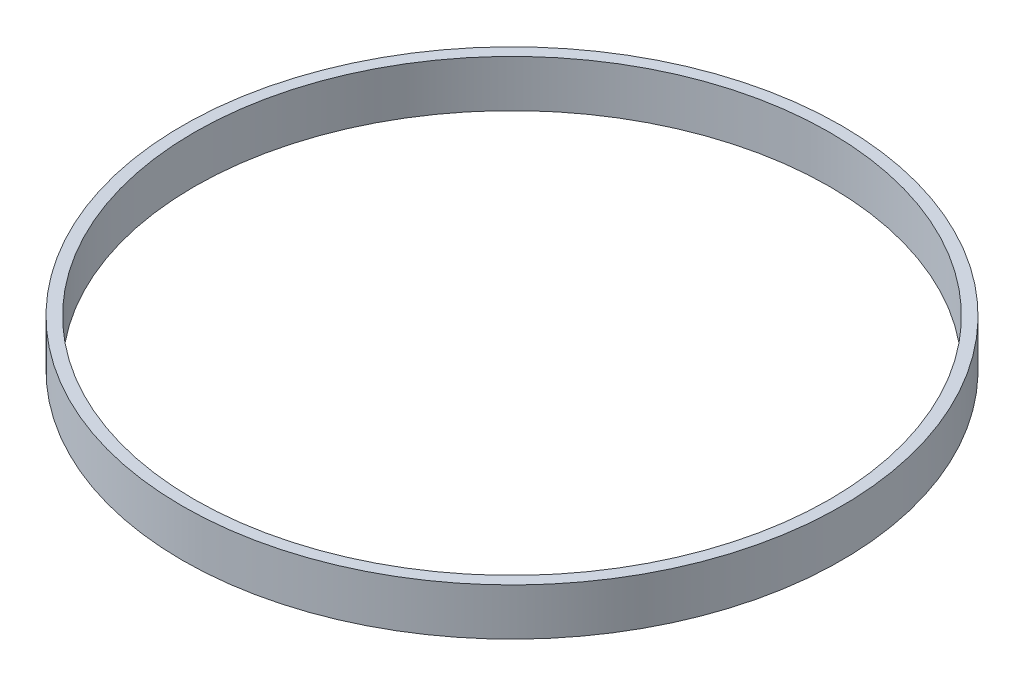
SolidWorks part; units mm, degrees
material "AISI 316 Stainless Steel Sheet (SS)"
ref_plane "Front Plane" through (0, 0, 0) normal (0, 0, 1) x (1, 0, 0)
ref_plane "Top Plane" through (0, 0, 0) normal (0, 1, 0) x (1, 0, 0)
ref_plane "Right Plane" through (0, 0, 0) normal (1, 0, 0) x (0, 0, -1)
sketch "Sketch1" plane through (0, 0, 0) normal (0, 1, 0) x (1, 0, 0)
  circle A0 centre (0, 0) radius 85.9536
  circle A1 centre (0, 0) radius 89.1286
  dimension "D1" = 171.9072
  dimension "D2" = 3.175
extrude "Boss-Extrude1" add sketch "Sketch1" along normal mid plane 12.7
